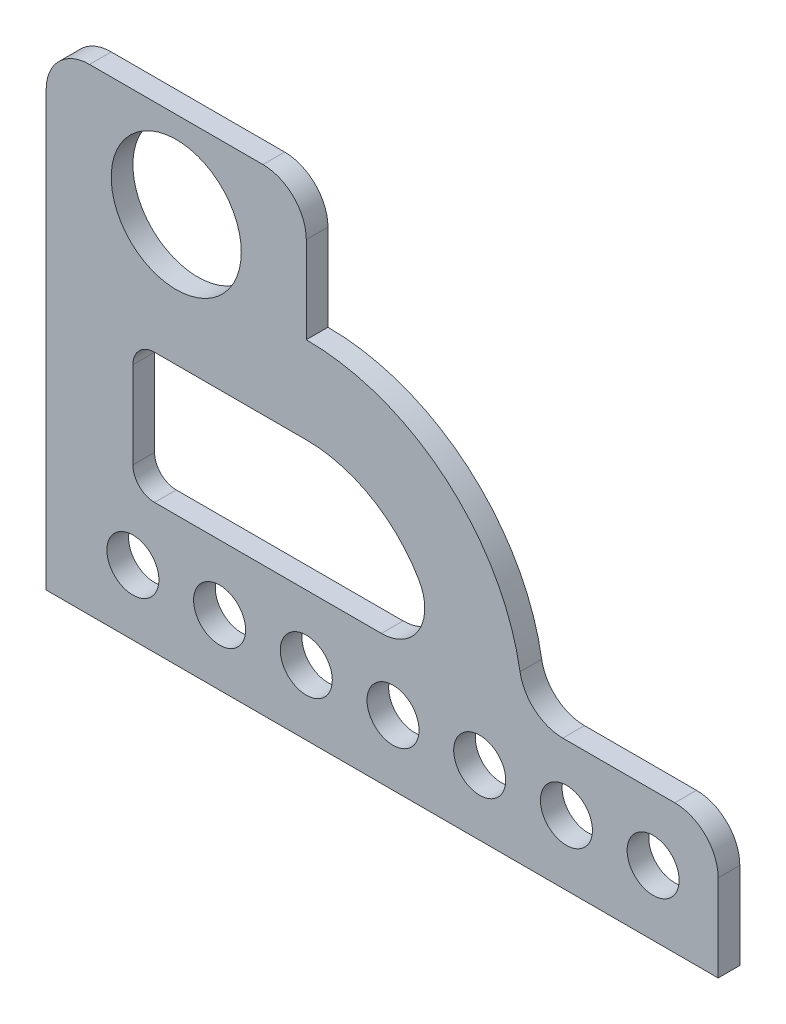
SolidWorks part; units mm, degrees
ref_plane "Front Plane" through (0, 0, 0) normal (0, 0, 1) x (1, 0, 0)
ref_plane "Top Plane" through (0, 0, 0) normal (0, 1, 0) x (1, 0, 0)
ref_plane "Right Plane" through (0, 0, 0) normal (1, 0, 0) x (0, 0, -1)
sketch "Sketch2" plane through (0, 0, 0) normal (0, 0, 1) x (1, 0, 0)
  line L0 (0, 0) -> (-155, 0)
  line L1 (-155, 0) -> (-155, 100)
  line L2 (-145, 110) -> (-105, 110)
  line L3 (-95, 100) -> (-95, 80)
  line L4 (0, 0) -> (0, 20)
  line L5 (-35.8392, 30) -> (-10, 30)
  line L6 (-95, 60) -> (-130, 60)
  line L7 (-135, 55) -> (-135, 35)
  line L8 (-130, 30) -> (-95, 30)
  line L9 (-95, 30) -> (-77.6795, 30)
  arc A0 (-45.6993, 38.3333) -> (-95, 80) centre (-95, 30) ccw
  arc A1 (-69.0192, 45) -> (-95, 60) centre (-95, 30) ccw
  circle A2 centre (-125, 90) radius 15
  circle A3 centre (-135, 15) radius 6
  circle A4 centre (-115, 15) radius 6
  circle A5 centre (-95, 15) radius 6
  circle A6 centre (-75, 15) radius 6
  circle A7 centre (-55, 15) radius 6
  circle A8 centre (-35, 15) radius 6
  circle A9 centre (-15, 15) radius 6
  arc A10 (-155, 100) -> (-145, 110) centre (-145, 100) cw
  arc A11 (-105, 110) -> (-95, 100) centre (-105, 100) cw
  arc A12 (0, 20) -> (-10, 30) centre (-10, 20) ccw
  arc A13 (-130, 30) -> (-135, 35) centre (-130, 35) cw
  arc A14 (-135, 55) -> (-130, 60) centre (-130, 55) cw
  arc A15 (-45, 30) -> (-95, 80) centre (-95, 30) ccw construction
  arc A16 (-35.8392, 30) -> (-45.6993, 38.3333) centre (-35.8392, 40) cw
  arc A17 (-65, 30) -> (-95, 60) centre (-95, 30) ccw construction
  arc A18 (-77.6795, 30) -> (-69.0192, 45) centre (-77.6795, 40) ccw
  point P38 (-155, 110)
  point P41 (-95, 110)
  point P44 (0, 30)
  point P47 (-135, 30)
  point P53 (-45, 30)
  point P57 (-65, 30)
  dimension "D5" = 50
  dimension "D8" = 30
  dimension "D10" = 12
  dimension "D15" = 10
  dimension "D16" = 10
  dimension "D17" = 10
  dimension "D18" = 5
  dimension "D19" = 5
  dimension "D20" = 10
  dimension "D21" = 10
  dimension "D1" = 110
  dimension "D2" = 155
  dimension "D3" = 30
  dimension "D4" = 60
  dimension "D6" = 20
  dimension "D7" = 30
  dimension "D9" = 20
  dimension "D11" = 15
  dimension "D13" = 20
  dimension "D14" = 20
  dimension "D12" = 7
extrude "Boss-Extrude1" add sketch "Sketch2" along normal blind 5
